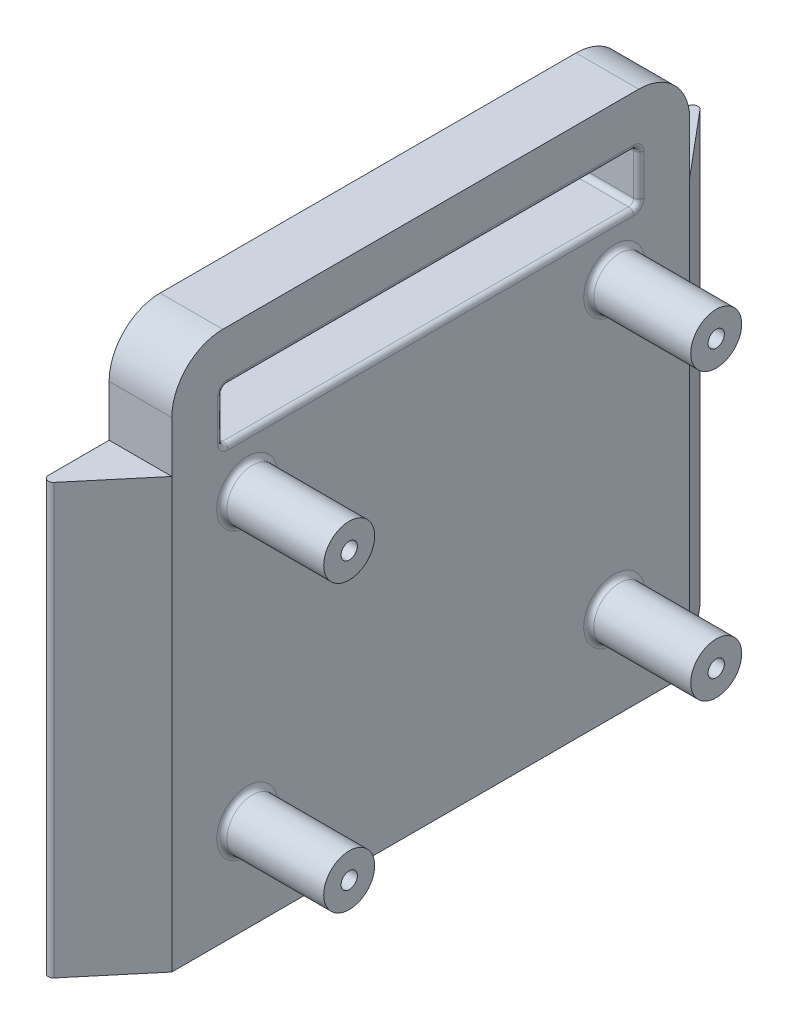
SolidWorks part; units mm, degrees
ref_plane "Front Plane" through (0, 0, 0) normal (0, 0, 1) x (1, 0, 0)
ref_plane "Top Plane" through (0, 0, 0) normal (0, 1, 0) x (1, 0, 0)
ref_plane "Right Plane" through (0, 0, 0) normal (1, 0, 0) x (0, 0, -1)
sketch "Sketch2" plane through (0, 0, 0) normal (0, 1, 0) x (1, 0, 0)
  line L0 (12.3, -50.8) -> (12.3, 50.8)
  line L1 (0, -65.4586) -> (0, 65.4586)
  line L2 (0, 65.4586) -> (12.3, 50.8)
  line L3 (0, -65.4586) -> (12.3, -50.8)
  point P2 (12.3, 0)
  point P5 (0, 0)
  dimension "D1" = 40
  dimension "D3" = 101.6
  dimension "D4" = 12.3
extrude "Boss-Extrude1" add sketch "Sketch2" along normal blind 114.2
sketch "Sketch4" plane through (12.3, 0, 0) normal (1, 0, 0) x (0, 0, -1)
  line L0 (-36, 48.2) -> (36, 48.2) construction
  line L1 (-50.8, 114.2) -> (50.8, 114.2) construction
  circle A0 centre (-36, 104.2) radius 5
  circle A1 centre (36, 104.2) radius 5
  circle A2 centre (36, 48.2) radius 5
  circle A3 centre (-36, 48.2) radius 5
  point P8 (0, 48.2)
  dimension "D3" = 10
  dimension "D4" = 10
  dimension "D5" = 10
  dimension "D6" = 10
  dimension "D1" = 72
  dimension "D2" = 56
  dimension "D7" = 10
extrude "Boss-Extrude2" add sketch "Sketch4" along normal blind 20
sketch "Sketch5" plane through (32.3, 0, 0) normal (1, 0, 0) x (0, 0, -1)
  point P0 (-36, 104.2)
  point P1 (36, 104.2)
  point P3 (36, 48.2)
  point P5 (-36, 48.2)
hole_wizard "Ø5.0mm Dowel Hole1" positions "Sketch5" profile "Sketch6" hole size "Ø5.0" standard "ANSI Metric"
sketch "Sketch6" plane through (32.3, 104.2, 36) normal (0, 1, 0) x (0, 0, -1)
  line L0 (0, 0) -> (0, 10)
  line L1 (0, 10) -> (1.6, 10)
  line L2 (1.6, 10) -> (1.6, 0)
  line L5 (1.6, 0) -> (0, 0)
  line L10 (0, 10) -> (-1.6, 10) construction
  line L11 (0, -6.35) -> (0, 107.95) construction
  dimension "Hole Dia." = 3.2
  dimension "Hole Depth" = 10
  dimension "Drill Angle" = 180
sketch "Sketch8" plane through (0, 0, 0) normal (1, 0, 0) x (0, 0, -1)
  line L0 (50.8, 114.2) -> (50.8, 0) construction
  line L1 (-50.8, 114.2) -> (-40.8, 114.2)
  line L2 (-50.8, 114.2) -> (-50.8, 134.2)
  line L3 (-50.8, 134.2) -> (50.8, 134.2)
  line L4 (50.8, 114.2) -> (50.8, 134.2)
  line L5 (40.8, 114.2) -> (50.8, 114.2)
  line L7 (-40.8, 114.2) -> (-40.8, 124.2)
  line L8 (-40.8, 124.2) -> (40.8, 124.2)
  line L9 (40.8, 114.2) -> (40.8, 124.2)
  dimension "D1" = 10
  dimension "D2" = 10
  dimension "D3" = 10
  dimension "D4" = 10
extrude "Boss-Extrude3" add sketch "Sketch8" along normal up to surface (12.3 mm away) up to face at (12.3, 48.2, 41)
fillet "Fillet1" radius 10 2 edges at (6.15, 134.2, -50.8) (6.15, 134.2, 50.8)
fillet "Fillet2" radius 1 18 edges at (0, 57.1, 65.4586) (12.3, 119.2, -40.8) (0, 119.2, -40.8) (12.3, 124.2, 0) (0, 124.2, 0) (12.3, 114.2, 0) (12.3, 48.2, -31) (12.3, 48.2, 41) (12.3, 104.2, 41) (12.3, 104.2, -31) (12.3, 119.2, 40.8) (0, 119.2, 40.8) (6.15, 114.2, -40.8) (6.15, 124.2, -40.8) (6.15, 124.2, 40.8) (6.15, 114.2, 40.8) (0, 57.1, -65.4586) (0, 114.2, 0)
ref_plane "Plane1" through (12.3, 0, -50.8) normal (0, 0, -1) x (-1, 0, 0)
sketch "Sketch10" plane through (0, 0, 0) normal (0, -1, 0) x (1, 0, 0)
  line L0 (12.3, -50.8) -> (1.766, -63.3539) construction
  line L1 (0, -62.7111) -> (0, 62.7111) construction
  line L2 (1.766, 63.3539) -> (12.3, 50.8) construction
  line L3 (12.3, 50.8) -> (12.3, -50.8) construction
  line L4 (12.3, -50.8) -> (1.766, -63.3539)
  line L5 (0, -62.7111) -> (0, 62.7111)
  line L6 (1.766, 63.3539) -> (12.3, 50.8)
  line L7 (12.3, 50.8) -> (12.3, -50.8)
  arc A0 (0, -62.7111) -> (1.766, -63.3539) centre (1, -62.7111) ccw construction
  arc A1 (1.766, 63.3539) -> (0, 62.7111) centre (1, 62.7111) ccw construction
  arc A2 (0, -62.7111) -> (1.766, -63.3539) centre (1, -62.7111) ccw
  arc A3 (1.766, 63.3539) -> (0, 62.7111) centre (1, 62.7111) ccw
extrude "Cut-Extrude1" cut sketch "Sketch10" against normal blind 30
equation "\"mount_diameter\"=10"
equation "\"D3@Sketch4\"=\"mount_diameter\""
equation "\"D4@Sketch4\"=\"mount_diameter\""
equation "\"D5@Sketch4\"=\"mount_diameter\""
equation "\"D6@Sketch4\"=\"mount_diameter\""
